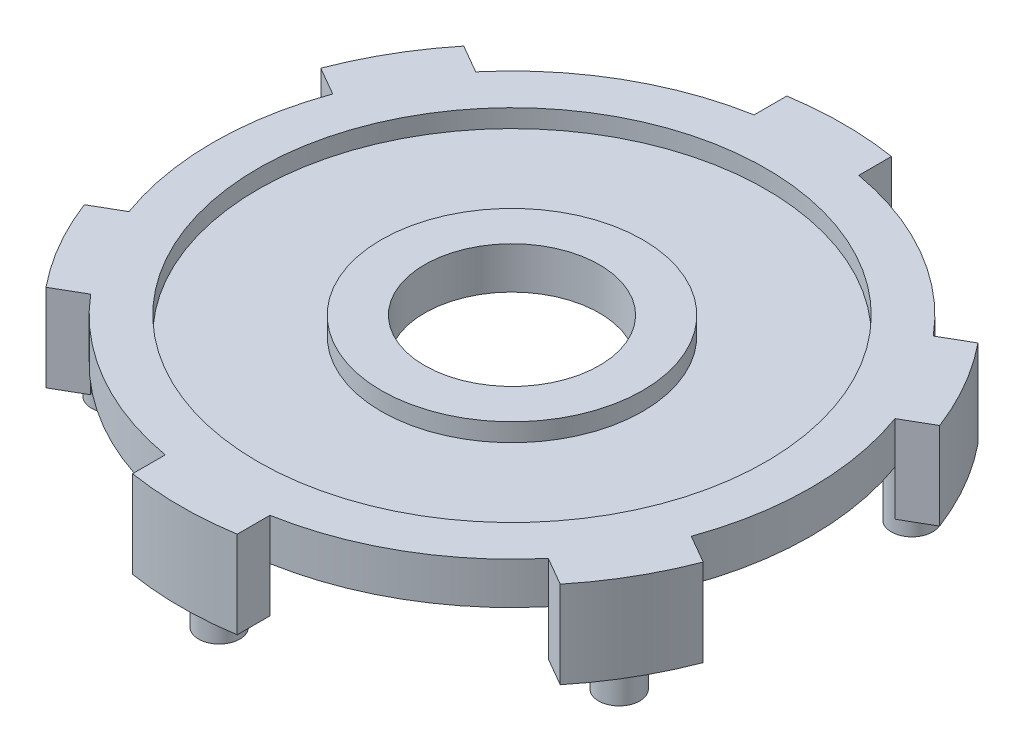
SolidWorks part; units mm, degrees
material "ABS"
ref_plane "Front Plane" through (0, 0, 0) normal (0, 0, 1) x (1, 0, 0)
ref_plane "Top Plane" through (0, 0, 0) normal (0, 1, 0) x (1, 0, 0)
ref_plane "Right Plane" through (0, 0, 0) normal (1, 0, 0) x (0, 0, -1)
sketch "Sketch1" plane through (0, 0, 0) normal (0, 1, 0) x (1, 0, 0)
  circle A0 centre (0, 0) radius 13.4239
  dimension "D1" = 26.8478
extrude "Boss-Extrude1" add sketch "Sketch1" along normal blind 1.8796
sketch "Sketch2" plane through (0, 1.8796, 0) normal (0, 1, 0) x (1, 0, 0)
  line L0 (-13.8923, 5.3077) -> (-4.699, 0)
  line L2 (2.3495, -14.6849) -> (2.3495, -4.0695)
  line L4 (-2.3495, -14.6849) -> (-2.3495, -4.0695)
  line L7 (-11.5428, 9.3772) -> (-2.3495, 4.0695)
  line L8 (11.5428, 9.3772) -> (2.3495, 4.0695)
  line L9 (13.8923, 5.3077) -> (4.699, 0)
  line L10 (2.3495, 4.0695) -> (2.3495, 14.6849)
  line L11 (4.699, 0) -> (13.8923, -5.3077)
  line L12 (-2.3495, 4.0695) -> (-2.3495, 14.6849)
  line L14 (-4.699, 0) -> (-13.8923, -5.3077)
  line L15 (-2.3495, -4.0695) -> (-11.5428, -9.3772)
  line L16 (2.3495, -4.0695) -> (11.5428, -9.3772)
  arc A0 (-2.3495, -14.6849) -> (2.3495, -14.6849) centre (0, 0) ccw
  arc A1 (2.3495, 14.6849) -> (-2.3495, 14.6849) centre (0, 0) ccw
  arc A2 (11.5428, -9.3772) -> (13.8923, -5.3077) centre (0, 0) ccw
  arc A3 (-11.5428, 9.3772) -> (-13.8923, 5.3077) centre (0, 0) ccw
  arc A4 (-13.8923, -5.3077) -> (-11.5428, -9.3772) centre (0, 0) ccw
  arc A5 (13.8923, 5.3077) -> (11.5428, 9.3772) centre (0, 0) ccw
  point P0 (0, 0)
  point P18 (0, 0)
  dimension "D2" = 14.6849
  dimension "D1" = 4.699
  dimension "D5" = 4.699
  dimension "D3" = 3
extrude "Boss-Extrude2" add sketch "Sketch2" against normal blind 1.8796
sketch "Sketch3" plane through (0, 1.8796, 0) normal (0, 1, 0) x (1, 0, 0)
  circle A0 centre (0, 0) radius 11.4046
  circle A1 centre (0, 0) radius 5.8674
  dimension "D1" = 22.8092
  dimension "D2" = 11.7348
extrude "Cut-Extrude1" cut sketch "Sketch3" against normal blind 0.8128 contours A0
sketch "Sketch4" plane through (0, 1.0668, 0) normal (0, 1, 0) x (1, 0, 0)
  circle A0 centre (0, 0) radius 5.8674
  dimension "D1" = 11.7348
extrude "Boss-Extrude3" add sketch "Sketch4" along normal up to surface (0.8128 mm away) up to face at (0, 1.8796, 11.4046)
sketch "Sketch5" plane through (0, 1.8796, 0) normal (0, 1, 0) x (1, 0, 0)
  circle A0 centre (0, 0) radius 3.9243
  dimension "D1" = 7.8486
extrude "Cut-Extrude2" cut sketch "Sketch5" against normal through all
sketch "Sketch6" plane through (0, 0, 0) normal (0, -1, 0) x (1, 0, 0)
  circle A0 centre (0, 0) radius 7.7216
  dimension "D1" = 15.4432
extrude "Boss-Extrude4" add sketch "Sketch6" along normal blind 1.778
sketch "Sketch7" plane through (0, -1.778, 0) normal (0, -1, 0) x (1, 0, 0)
  circle A0 centre (0, 0) radius 6.5532
  dimension "D1" = 13.1064
extrude "Cut-Extrude3" cut sketch "Sketch7" against normal blind 1.778
sketch "Sketch8" plane through (0, 0, 0) normal (0, -1, 0) x (1, 0, 0)
  line L12 (-2.3495, -13.2167) -> (-2.3495, -14.6849)
  line L13 (2.3495, -14.6849) -> (2.3495, -13.2167)
  line L14 (10.2712, -8.6431) -> (11.5428, -9.3772)
  line L15 (13.8923, -5.3077) -> (12.6207, -4.5736)
  line L16 (12.6207, 4.5736) -> (13.8923, 5.3077)
  line L17 (11.5428, 9.3772) -> (10.2712, 8.6431)
  line L18 (2.3495, 13.2167) -> (2.3495, 14.6849)
  line L19 (-2.3495, 14.6849) -> (-2.3495, 13.2167)
  line L20 (-10.2712, 8.6431) -> (-11.5428, 9.3772)
  line L21 (-13.8923, 5.3077) -> (-12.6207, 4.5736)
  line L22 (-12.6207, -4.5736) -> (-13.8923, -5.3077)
  line L23 (-11.5428, -9.3772) -> (-10.2712, -8.6431)
  line L24 (-2.3495, -13.2167) -> (-2.3495, -14.6849)
  line L25 (2.3495, -14.6849) -> (2.3495, -13.2167)
  line L26 (10.2712, -8.6431) -> (11.5428, -9.3772)
  line L27 (13.8923, -5.3077) -> (12.6207, -4.5736)
  line L28 (12.6207, 4.5736) -> (13.8923, 5.3077)
  line L29 (11.5428, 9.3772) -> (10.2712, 8.6431)
  line L30 (2.3495, 13.2167) -> (2.3495, 14.6849)
  line L31 (-2.3495, 14.6849) -> (-2.3495, 13.2167)
  line L32 (-10.2712, 8.6431) -> (-11.5428, 9.3772)
  line L33 (-13.8923, 5.3077) -> (-12.6207, 4.5736)
  line L34 (-12.6207, -4.5736) -> (-13.8923, -5.3077)
  line L35 (-11.5428, -9.3772) -> (-10.2712, -8.6431)
  arc A0 (-10.2712, 8.6431) -> (-12.6207, 4.5736) centre (0, 0) ccw
  arc A1 (-2.3495, 13.2167) -> (-10.2712, 8.6431) centre (0, 0) ccw construction
  arc A2 (2.3495, 13.2167) -> (-2.3495, 13.2167) centre (0, 0) ccw
  arc A3 (12.6207, 4.5736) -> (10.2712, 8.6431) centre (0, 0) ccw
  arc A4 (10.2712, -8.6431) -> (12.6207, -4.5736) centre (0, 0) ccw
  arc A5 (-2.3495, -13.2167) -> (2.3495, -13.2167) centre (0, 0) ccw
  arc A6 (-12.6207, -4.5736) -> (-10.2712, -8.6431) centre (0, 0) ccw
  arc A14 (-10.2712, -8.6431) -> (-2.3495, -13.2167) centre (0, 0) ccw
  arc A15 (-2.3495, -14.6849) -> (2.3495, -14.6849) centre (0, 0) ccw
  arc A16 (2.3495, -13.2167) -> (10.2712, -8.6431) centre (0, 0) ccw
  arc A17 (11.5428, -9.3772) -> (13.8923, -5.3077) centre (0, 0) ccw
  arc A18 (12.6207, -4.5736) -> (12.6207, 4.5736) centre (0, 0) ccw
  arc A19 (13.8923, 5.3077) -> (11.5428, 9.3772) centre (0, 0) ccw
  arc A20 (10.2712, 8.6431) -> (2.3495, 13.2167) centre (0, 0) ccw
  arc A21 (2.3495, 14.6849) -> (-2.3495, 14.6849) centre (0, 0) ccw
  arc A22 (-2.3495, 13.2167) -> (-10.2712, 8.6431) centre (0, 0) ccw
  arc A23 (-11.5428, 9.3772) -> (-13.8923, 5.3077) centre (0, 0) ccw
  arc A24 (-12.6207, 4.5736) -> (-12.6207, -4.5736) centre (0, 0) ccw
  arc A25 (-13.8923, -5.3077) -> (-11.5428, -9.3772) centre (0, 0) ccw
  arc A27 (-2.3495, -14.6849) -> (2.3495, -14.6849) centre (0, 0) ccw
  arc A29 (11.5428, -9.3772) -> (13.8923, -5.3077) centre (0, 0) ccw
  arc A31 (13.8923, 5.3077) -> (11.5428, 9.3772) centre (0, 0) ccw
  arc A33 (2.3495, 14.6849) -> (-2.3495, 14.6849) centre (0, 0) ccw
  arc A35 (-11.5428, 9.3772) -> (-13.8923, 5.3077) centre (0, 0) ccw
  arc A37 (-13.8923, -5.3077) -> (-11.5428, -9.3772) centre (0, 0) ccw
  dimension "D1" = 0
extrude "Boss-Extrude5" add sketch "Sketch8" along normal blind 2.032
sketch "Sketch9" plane through (0, 0, 0) normal (0, -1, 0) x (1, 0, 0)
  line L1 (-11.3835, -6.5722) -> (11.3835, 6.5723) construction
  line L2 (0, 13.1445) -> (0, -13.1445) construction
  circle A0 centre (0, 0) radius 13.1445 construction
  circle A1 centre (0, 13.1445) radius 0.9271
  arc A2 (12.6207, 4.5736) -> (10.2712, 8.6431) centre (0, 0) ccw construction
  point P17 (11.6254, 6.7119)
  dimension "D1" = 26.289
  dimension "D2" = 1.8542
  dimension "D5" = 60
extrude "Boss-Extrude6" add sketch "Sketch9" along normal blind 3.683
pattern_circular "CirPattern1" count 6 over 360 about axis through (0, 0, 0) along (0, 1, 0) of "Boss-Extrude6"
